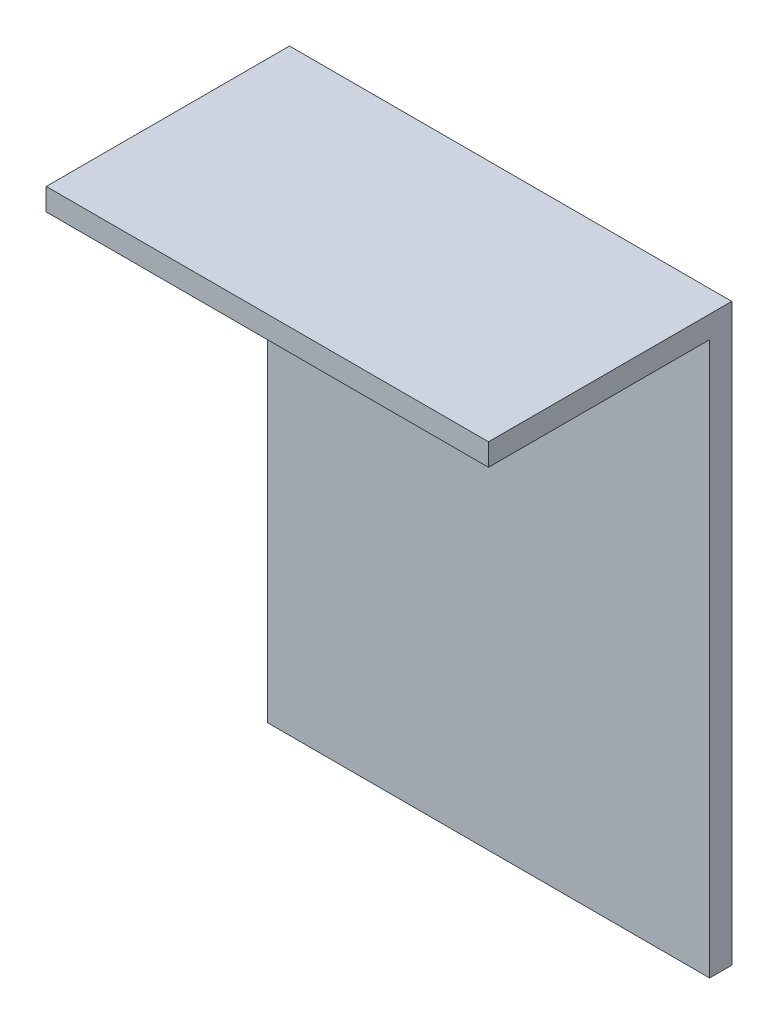
SolidWorks part; units mm, degrees
ref_plane "Front Plane" through (0, 0, 0) normal (0, 0, 1) x (1, 0, 0)
ref_plane "Top Plane" through (0, 0, 0) normal (0, 1, 0) x (1, 0, 0)
ref_plane "Right Plane" through (0, 0, 0) normal (1, 0, 0) x (0, 0, -1)
sketch "Sketch1" plane through (0, 0, 0) normal (0, 0, 1) x (1, 0, 0)
  line L1 (0, 0) -> (50.8, 0)
  line L2 (0, 0) -> (0, 66.04)
  line L3 (0, 66.04) -> (50.8, 66.04)
  line L4 (50.8, 0) -> (50.8, 66.04)
  dimension "D1" = 66.04
  dimension "D2" = 50.8
extrude "Boss-Extrude1" add sketch "Sketch1" along normal blind 2.54
sketch "Sketch2" plane through (0, 0, 2.54) normal (0, 0, 1) x (1, 0, 0)
  line L0 (50.8, 0) -> (50.8, 66.04) construction
  line L1 (0, 66.04) -> (50.8, 66.04)
  line L2 (0, 66.04) -> (0, 63.5)
  line L3 (0, 63.5) -> (50.8, 63.5)
  line L4 (50.8, 66.04) -> (50.8, 63.5)
  dimension "D1" = 2.54
extrude "Boss-Extrude2" add sketch "Sketch2" along normal blind 25.4
